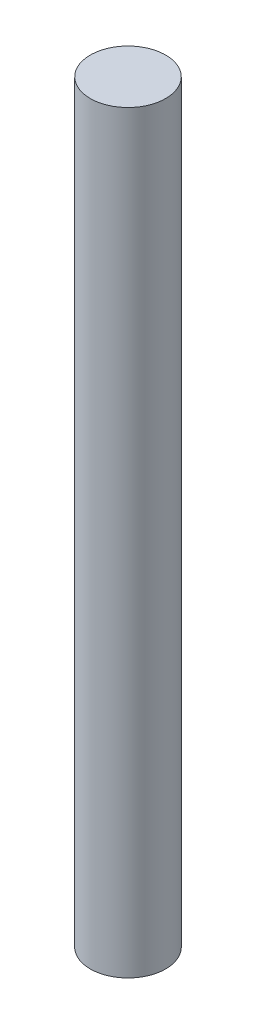
SolidWorks part; units mm, degrees
ref_plane "Front Plane" through (0, 0, 0) normal (0, 0, 1) x (1, 0, 0)
ref_plane "Top Plane" through (0, 0, 0) normal (0, 1, 0) x (1, 0, 0)
ref_plane "Right Plane" through (0, 0, 0) normal (1, 0, 0) x (0, 0, -1)
sketch "Sketch1" plane through (0, 0, 0) normal (0, 1, 0) x (1, 0, 0)
  circle A0 centre (0, 0) radius 2.5
extrude "Boss-Extrude1" add sketch "Sketch1" along normal blind 50
